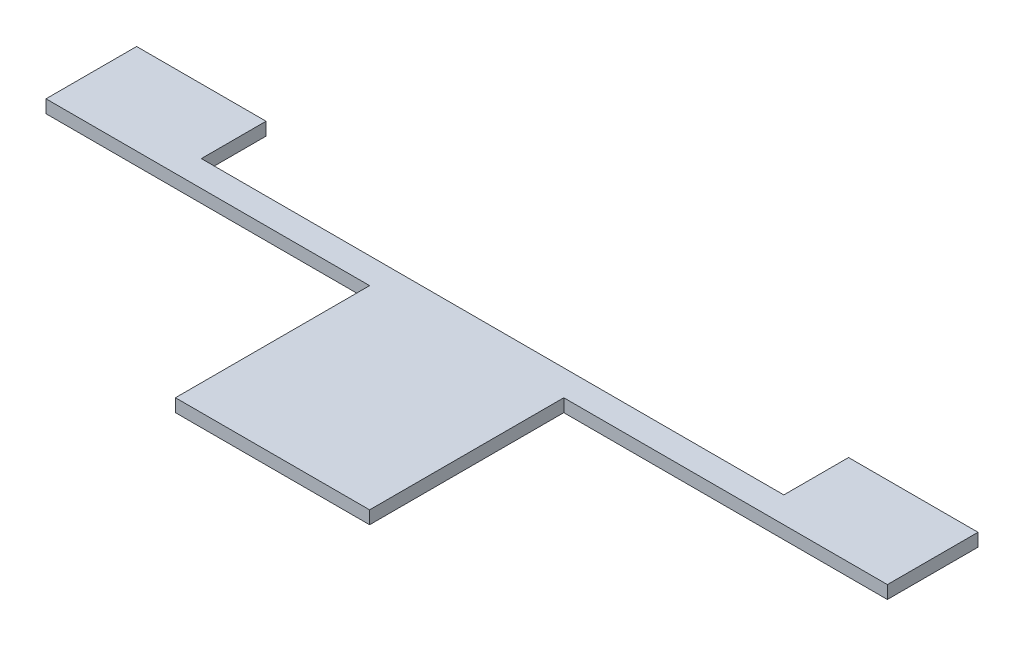
SolidWorks part; units mm, degrees
ref_plane "Front Plane" through (0, 0, 0) normal (0, 0, 1) x (1, 0, 0)
ref_plane "Top Plane" through (0, 0, 0) normal (0, 1, 0) x (1, 0, 0)
ref_plane "Right Plane" through (0, 0, 0) normal (1, 0, 0) x (0, 0, -1)
sketch "Sketch1" plane through (0, 0, 0) normal (0, 1, 0) x (1, 0, 0)
  line L0 (-78.5983, 23.8626) -> (-78.5983, 37.8626)
  line L1 (-78.5983, 37.8626) -> (51.4017, 37.8626)
  line L2 (-78.5983, 37.8626) -> (-78.5983, 23.8626)
  line L3 (-78.5983, 23.8626) -> (51.4017, 23.8626)
  line L4 (51.4017, 37.8626) -> (51.4017, 23.8626)
  line L5 (-78.5983, 37.8626) -> (-58.5983, 37.8626)
  line L6 (-58.5983, 37.8626) -> (-58.5983, 27.8626)
  line L7 (-58.5983, 27.8626) -> (31.4017, 27.8626)
  line L8 (31.4017, 27.8626) -> (31.4017, 37.8626)
  line L9 (31.4017, 37.8626) -> (51.4017, 37.8626)
  line L10 (51.4017, 23.8626) -> (-78.5983, 23.8626)
  line L11 (-78.5983, 23.8626) -> (-78.5983, 37.8626)
  line L12 (-78.5983, 23.8626) -> (-28.5983, 23.8626)
  line L13 (-28.5983, 23.8626) -> (-28.5983, -6.1374)
  line L14 (-28.5983, -6.1374) -> (1.4017, -6.1374)
  line L15 (1.4017, -6.1374) -> (1.4017, 23.8626)
  line L16 (1.4017, 23.8626) -> (51.4017, 23.8626)
extrude "Boss-Extrude1" add sketch "Sketch1" along normal blind 2 contours L8 L7 L6 L1 L0 L3 L10 L4 | L14 L15 L10 L13
